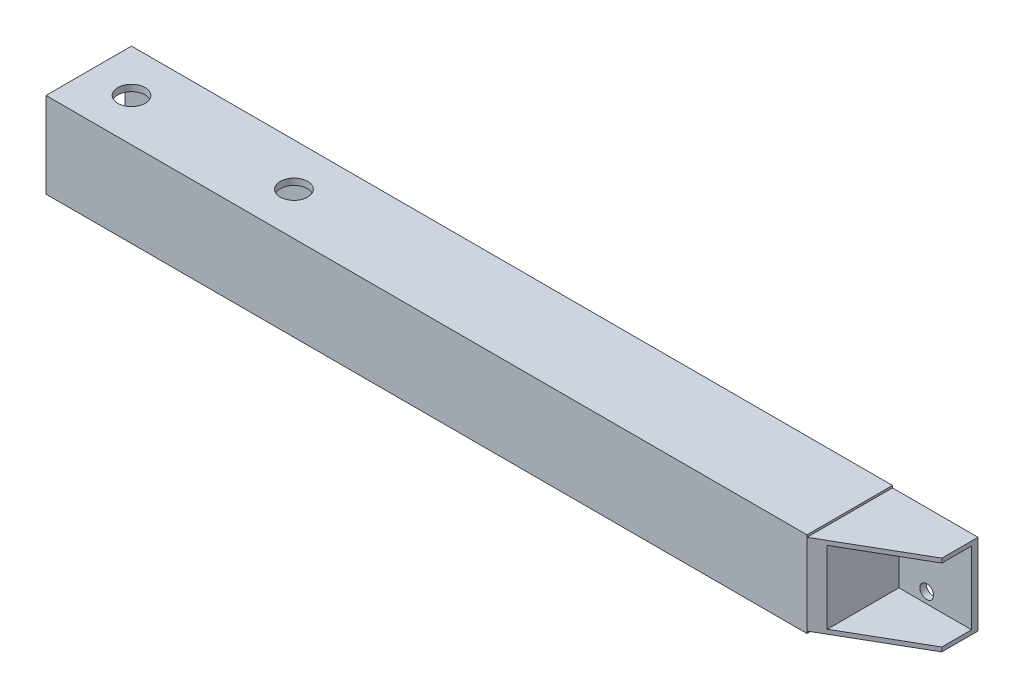
SolidWorks part; units mm, degrees
ref_plane "Plan de face" through (0, 0, 0) normal (0, 0, 1) x (1, 0, 0)
ref_plane "Plan de dessus" through (0, 0, 0) normal (0, 1, 0) x (1, 0, 0)
ref_plane "Plan de droite" through (0, 0, 0) normal (1, 0, 0) x (0, 0, -1)
sketch "Esquisse1" plane through (0, 0, 0) normal (0, 0, 1) x (1, 0, 0)
  line L1 (-89, -10) -> (89, -10)
  line L2 (-89, -10) -> (-89, 10)
  line L3 (-89, 10) -> (89, 10)
  line L4 (89, -10) -> (89, 10)
  line L5 (-89, -10) -> (89, 10) construction
  line L6 (-89, 10) -> (89, -10) construction
  line L7 (89, 10) -> (109, 10)
  line L8 (89, 10) -> (89, -10)
  line L9 (89, -10) -> (109, -10)
  line L10 (109, 10) -> (109, -10)
  point P0 (0, 0)
  dimension "D1" = 178
  dimension "D2" = 20
  dimension "D3" = 20
extrude "Boss.-Extru.1" add sketch "Esquisse1" along normal blind 20 contours L1 L4 L3 L2 | L10 L7 L4 L9
sketch "Esquisse3" plane through (-89, 0, 0) normal (-1, 0, 0) x (0, 0, 1)
  line L0 (20, 10) -> (0, 10) construction
  line L1 (0, 10) -> (20, 10)
  line L2 (0, 10) -> (0, -10)
  line L3 (0, -10) -> (20, -10)
  line L4 (20, 10) -> (20, -10)
  line L5 (0, 10) -> (20, -10) construction
  line L6 (20, -10) -> (20.0166, -9.9013) construction
  line L7 (20, 10) -> (0, -10) construction
  line L9 (1.5, -8.5) -> (18.5, -8.5)
  line L10 (1.5, -8.5) -> (1.5, 8.5)
  line L11 (1.5, 8.5) -> (18.5, 8.5)
  line L12 (18.5, -8.5) -> (18.5, 8.5)
  line L13 (1.5, -8.5) -> (18.5, 8.5) construction
  line L14 (1.5, 8.5) -> (18.5, -8.5) construction
  point P7 (10, 0)
  dimension "D1" = 17
extrude "Enlèv. mat.-Extru.1" cut sketch "Esquisse3" against normal blind 178 contours L11 L12 L9 L10
sketch "Esquisse4" plane through (0, 0, 20) normal (0, 0, 1) x (1, 0, 0)
  line L0 (109, 10) -> (109, -10) construction
  line L1 (109, 8.5) -> (92, 8.5)
  line L2 (109, 8.5) -> (109, -8.5)
  line L3 (109, -8.5) -> (92, -8.5)
  line L4 (92, 8.5) -> (92, -8.5)
  line L5 (92, 8.5) -> (109, -8.5) construction
  line L6 (109, 8.5) -> (92, -8.5) construction
  line L7 (109, 0) -> (58.4645, 0) construction
  point P9 (100.5, 0)
  dimension "D1" = 17
  dimension "D2" = 17
extrude "Enlèv. mat.-Extru.2" cut sketch "Esquisse4" against normal blind 18.5
chamfer "Chanfrein1" distance 20 angle 30 1 edges at (109, 9.25, 20)
sketch "Esquisse5" plane through (0, 0, 0) normal (0, 0, -1) x (-1, 0, 0)
  line L0 (-109, 0) -> (-86.1661, 0) construction
  line L1 (-109, 10) -> (-109, -10) construction
  line L2 (89, -10) -> (-109, -10) construction
  line L3 (-109, 9.5) -> (-89, 9.5)
  line L4 (-109, 9.5) -> (-109, -9.5)
  line L5 (-109, -9.5) -> (-89, -9.5)
  line L6 (-89, 9.5) -> (-89, -9.5)
  line L7 (-109, 9.5) -> (-89, -9.5) construction
  line L8 (-109, -9.5) -> (-89, 9.5) construction
  line L9 (-109, 10) -> (-89, 10)
  line L10 (-109, 10) -> (-109, -10)
  line L11 (-109, -10) -> (-89, -10)
  line L12 (-89, 10) -> (-89, -10)
  point P5 (-99, 0)
  line M4 (-109, -10) -> (89, -10)
  line M6 (89, 10) -> (-109, 10)
  line M7 (-109, 10) -> (-109, -10)
  dimension "D1" = 20
  dimension "D2" = 19
extrude "Enlèv. mat.-Extru.3" cut sketch "Esquisse5" against normal blind 24 contours L12 L3 M6 M7 | L12 L5 M7 M4
sketch "Esquisse6" plane through (0, 0, 0) normal (0, 0, -1) x (-1, 0, 0)
  line L0 (-105.6562, 0) -> (-82.7292, 0) construction
  line L2 (89, -10) -> (89, 10) construction
  circle A0 centre (-98.5, 6) radius 1.6
  circle A1 centre (-98.5, -6) radius 1.6
  dimension "D1" = 3.2
  dimension "D2" = 187.5
  dimension "D3" = 12
extrude "Enlèv. mat.-Extru.4" cut sketch "Esquisse6" against normal blind 24
sketch "Esquisse7" plane through (0, -10, 0) normal (0, -1, 0) x (1, 0, 0)
  line L0 (-89, 10) -> (-11.6575, 10) construction
  line L1 (-89, 20) -> (-89, 0) construction
  circle A0 centre (-79, 10) radius 3.2
  circle A1 centre (-41, 10) radius 3.2
  dimension "D1" = 6.4
  dimension "D2" = 6.4
  dimension "D3" = 38
  dimension "D4" = 10
extrude "Enlèv. mat.-Extru.5" cut sketch "Esquisse7" against normal blind 34
